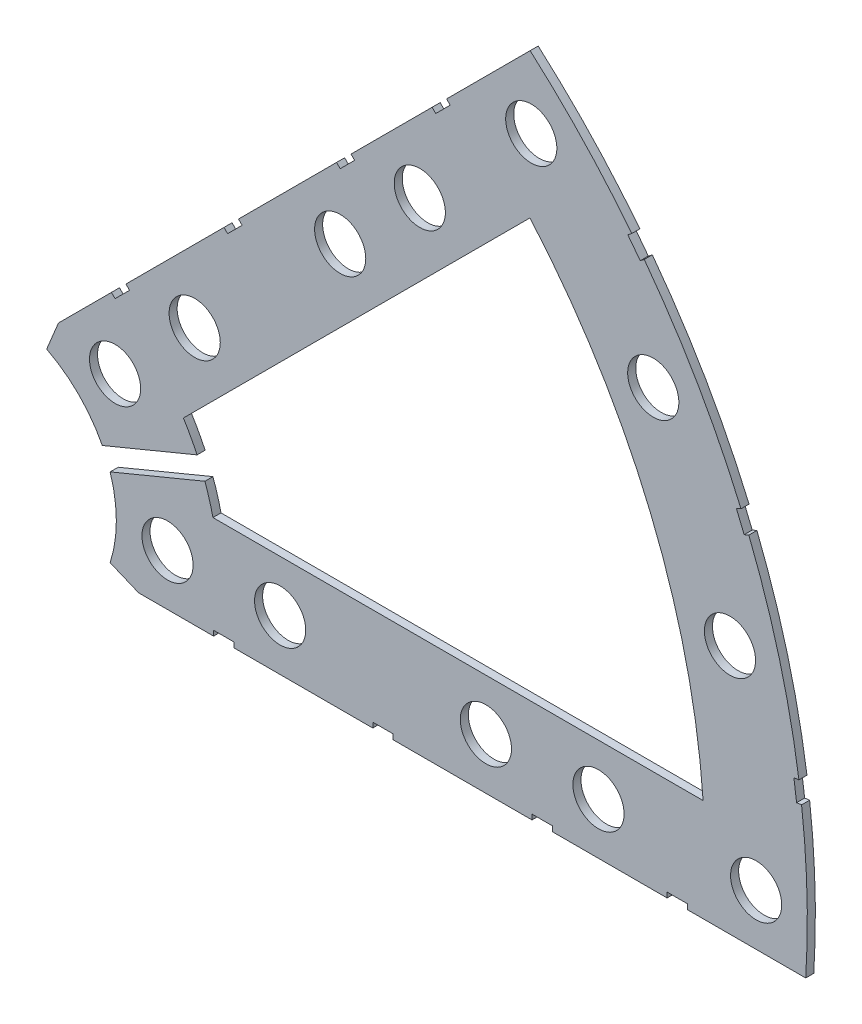
SolidWorks part; units mm, degrees
material "Copper"
ref_plane "Front Plane" through (0, 0, 0) normal (0, 0, 1) x (1, 0, 0)
ref_plane "Top Plane" through (0, 0, 0) normal (0, 1, 0) x (1, 0, 0)
ref_plane "Right Plane" through (0, 0, 0) normal (1, 0, 0) x (0, 0, -1)
sketch "Sketch1" plane through (0, 0, 0) normal (0, 0, 1) x (1, 0, 0)
  line L0 (0, 0) -> (320.3893, 0) construction
  line L1 (0, 0) -> (155.5285, 155.5285) construction
  line L2 (67.2115, 76.1917) -> (8.6967, 17.6769)
  line L3 (8.6967, 17.6769) -> (7.229, 14.1336)
  line L4 (101.4014, -6.35) -> (18.6489, -6.35)
  line L5 (15.1056, -4.8823) -> (18.6489, -6.35)
  line L6 (88.6729, 6.35) -> (27.8605, 6.35)
  line L9 (67.1914, 58.2111) -> (24.1905, 15.2102)
  line L10 (0, 0) -> (40.4486, 97.6516) construction
  line L11 (0, 0) -> (123.4567, -51.1374) construction
  line L18 (8.6967, 17.6769) -> (13.294, 8.6183) construction
  line L19 (18.6489, -6.35) -> (15.4943, 3.3063) construction
  line L20 (27.8605, 6.35) -> (27.7442, 6.7059) construction
  line L21 (24.1905, 15.2102) -> (24.3599, 14.8764) construction
  arc A0 (7.229, 14.1336) -> (15.1056, -4.8823) centre (0, 0) cw
  arc A1 (67.2115, 76.1917) -> (101.4014, -6.35) centre (0, 0) cw
  arc A2 (24.1905, 15.2102) -> (27.8605, 6.35) centre (0, 0) cw
  arc A3 (67.1914, 58.2111) -> (88.6729, 6.35) centre (0, 0) cw
  arc A8 (13.294, 8.6183) -> (15.4943, 3.3063) centre (0, 0) cw construction
  arc A9 (24.3599, 14.8764) -> (27.7442, 6.7059) centre (0, 0) cw construction
  dimension "D1" = 45
  dimension "D3" = 6.35
  dimension "D4" = 15.875
  dimension "D7" = 22.5
  dimension "D8" = 101.6
  dimension "D11" = 12.7
  dimension "D12" = 12.7
  dimension "D2" = 6.35
  dimension "D5" = 67.5
  dimension "D9" = 1.27
  dimension "D10" = 1.27
  dimension "D6" = 12.7
extrude "Boss-Extrude1" add sketch "Sketch1" along normal blind 1
sketch "Sketch2" plane through (0, 0, 1) normal (0, 0, 1) x (1, 0, 0)
  line L0 (0, 0) -> (101.6, 0) construction
  line L1 (0, 0) -> (71.842, 71.842) construction
  line L3 (0, 0) -> (22.225, 0) construction
  line L4 (0, 0) -> (15.7154, 15.7154) construction
  line L5 (0, 0) -> (95.25, 0) construction
  line L6 (0, 0) -> (92.0044, 24.6525) construction
  arc A0 (101.4014, -6.35) -> (67.2115, 76.1917) centre (0, 0) ccw construction
  circle A1 centre (22.225, 0) radius 3.175
  arc A2 (15.1056, -4.8823) -> (7.229, 14.1336) centre (0, 0) ccw construction
  circle A3 centre (36.195, 0) radius 3.175
  circle A4 centre (61.722, 0) radius 3.175
  circle A5 centre (75.692, 0) radius 3.175
  circle A6 centre (95.25, 0) radius 3.175
  circle A7 centre (15.7154, 15.7154) radius 3.175
  circle A8 centre (25.5937, 25.5937) radius 3.175
  circle A9 centre (43.644, 43.644) radius 3.175
  circle A10 centre (53.5223, 53.5223) radius 3.175
  circle A11 centre (92.0044, 24.6525) radius 3.175
  circle A12 centre (82.4889, 47.625) radius 3.175
  circle A13 centre (67.3519, 67.3519) radius 3.175
  dimension "D3" = 6.35
  dimension "D1" = 45
  dimension "D2" = 6.35
  dimension "D4" = 6.35
  dimension "D5" = 13.97
  dimension "D7" = 13.97
  dimension "D9" = 45
  dimension "D10" = 15
  dimension "D11" = 25.527
  dimension "D12" = 19.558
  dimension "D6" = 2
  dimension "D8" = 4
extrude "Cut-Extrude1" cut sketch "Sketch2" against normal through all
sketch "Sketch3" plane through (0, 0, 1) normal (0, 0, 1) x (1, 0, 0)
  line L0 (15.2664, 24.2467) -> (17.0625, 26.0427)
  line L1 (15.2664, 24.2467) -> (15.7154, 23.7977)
  line L2 (17.0625, 26.0427) -> (17.5115, 25.5937)
  line L3 (15.7154, 23.7977) -> (17.5115, 25.5937)
  line L4 (67.2115, 76.1917) -> (8.6967, 17.6769) construction
  line L5 (44.9911, 53.9713) -> (43.195, 52.1753)
  line L6 (44.9911, 53.9713) -> (45.4401, 53.5223)
  line L7 (43.195, 52.1753) -> (43.644, 51.7263)
  line L8 (45.4401, 53.5223) -> (43.644, 51.7263)
  line L9 (27.94, -6.35) -> (30.48, -6.35)
  line L10 (27.94, -6.35) -> (27.94, -5.715)
  line L11 (30.48, -6.35) -> (30.48, -5.715)
  line L12 (27.94, -5.715) -> (30.48, -5.715)
  line L13 (18.6489, -6.35) -> (101.4014, -6.35) construction
  line L14 (67.437, -6.35) -> (69.977, -6.35)
  line L15 (67.437, -6.35) -> (67.437, -5.715)
  line L16 (69.977, -6.35) -> (69.977, -5.715)
  line L17 (67.437, -5.715) -> (69.977, -5.715)
  line L18 (29.2307, 38.211) -> (31.0268, 40.007)
  line L19 (29.2307, 38.211) -> (29.6797, 37.762)
  line L20 (31.0268, 40.007) -> (31.4758, 39.558)
  line L21 (29.6797, 37.762) -> (31.4758, 39.558)
  line L22 (56.845, 65.8253) -> (55.049, 64.0292)
  line L23 (56.845, 65.8253) -> (57.294, 65.3763)
  line L24 (55.049, 64.0292) -> (55.498, 63.5802)
  line L25 (57.294, 65.3763) -> (55.498, 63.5802)
  line L26 (47.6885, -6.35) -> (50.2285, -6.35)
  line L27 (47.6885, -6.35) -> (47.6885, -5.715)
  line L28 (50.2285, -6.35) -> (50.2285, -5.715)
  line L29 (47.6885, -5.715) -> (50.2285, -5.715)
  line L30 (84.201, -6.35) -> (86.741, -6.35)
  line L31 (84.201, -6.35) -> (84.201, -5.715)
  line L32 (86.741, -6.35) -> (86.741, -5.715)
  line L33 (84.201, -5.715) -> (86.741, -5.715)
  line L34 (0, 0) -> (100.7308, 13.2615) construction
  line L35 (0, 0) -> (93.8662, 38.8806) construction
  line L36 (0, 0) -> (80.6047, 61.8502) construction
  line L37 (0, 0) -> (101.6, 0) construction
  line L38 (99.9355, 14.4377) -> (100.267, 11.9194)
  line L39 (99.9355, 14.4377) -> (101.1946, 14.6035)
  line L40 (100.267, 11.9194) -> (101.5261, 12.0852)
  line L41 (101.1946, 14.6035) -> (101.5261, 12.0852)
  line L42 (99.9355, 14.4377) -> (101.5261, 12.0852) construction
  line L43 (100.267, 11.9194) -> (101.1946, 14.6035) construction
  line L44 (93.7655, 37.4643) -> (94.9388, 37.9503)
  line L45 (93.7655, 37.4643) -> (92.7935, 39.811)
  line L46 (94.9388, 37.9503) -> (93.9668, 40.297)
  line L47 (92.7935, 39.811) -> (93.9668, 40.297)
  line L48 (93.7655, 37.4643) -> (93.9668, 40.297) construction
  line L49 (94.9388, 37.9503) -> (92.7935, 39.811) construction
  line L50 (79.3278, 62.4712) -> (80.874, 60.456)
  line L51 (79.3278, 62.4712) -> (80.3354, 63.2443)
  line L52 (80.874, 60.456) -> (81.8816, 61.2292)
  line L53 (80.3354, 63.2443) -> (81.8816, 61.2292)
  line L54 (79.3278, 62.4712) -> (81.8816, 61.2292) construction
  line L55 (80.874, 60.456) -> (80.3354, 63.2443) construction
  line L56 (13.9793, 4.4158) -> (28.0592, 10.2479)
  line L57 (13.9793, 4.4158) -> (13.0073, 6.7624)
  line L58 (28.0592, 10.2479) -> (27.0872, 12.5945)
  line L59 (13.0073, 6.7624) -> (27.0872, 12.5945)
  line L60 (13.9793, 4.4158) -> (27.0872, 12.5945) construction
  line L61 (28.0592, 10.2479) -> (13.0073, 6.7624) construction
  circle A0 centre (15.7154, 15.7154) radius 3.175 construction
  circle A1 centre (43.644, 43.644) radius 3.175 construction
  circle A2 centre (22.225, 0) radius 3.175 construction
  circle A3 centre (61.722, 0) radius 3.175 construction
  arc A4 (101.4014, -6.35) -> (67.2115, 76.1917) centre (0, 0) ccw construction
  circle A9 centre (36.195, 0) radius 3.175 construction
  arc A10 (15.1056, -4.8823) -> (7.229, 14.1336) centre (0, 0) ccw construction
  circle A11 centre (75.692, 0) radius 3.175 construction
  circle A12 centre (25.5937, 25.5937) radius 3.175 construction
  circle A13 centre (53.5223, 53.5223) radius 3.175 construction
  point P75 (20.5332, 8.5051)
  dimension "D2" = 5.715
  dimension "D3" = 2.54
  dimension "D6" = 5.715
  dimension "D8" = 0.635
  dimension "D9" = 5.715
  dimension "D12" = 5.715
  dimension "D4" = 7.5
  dimension "D5" = 22.5
  dimension "D7" = 37.5
  dimension "D10" = 90
  dimension "D11" = 1.27
  dimension "D14" = 0.635
  dimension "D15" = 90
  dimension "D18" = 0.635
  dimension "D19" = 90
  dimension "D22" = 0.635
  dimension "D17" = 6.35
  dimension "D20" = 2.54
  dimension "D21" = 15.24
  dimension "D25" = 90
  dimension "D26" = 1.27
  dimension "D23" = 11.4935
  dimension "D16" = 8.509
  dimension "D24" = 11.4935
  dimension "D13" = 8.509
extrude "Cut-Extrude2" cut sketch "Sketch3" against normal through all
equation "\"CoilSep\"=1.005"
equation "\"D11@Sketch2\"=\"CoilSep\""
equation "\"CoilSep2\"= \"D12@Sketch2\""
equation "\"D23@Sketch3\"=\"CoilSep\"/2-.05"
equation "\"D16@Sketch3\"=\"CoilSep2\"/2-.05"
equation "\"D24@Sketch3\"=\"CoilSep\"/2-.05"
equation "\"D13@Sketch3\"=\"CoilSep2\"/2-.05"
